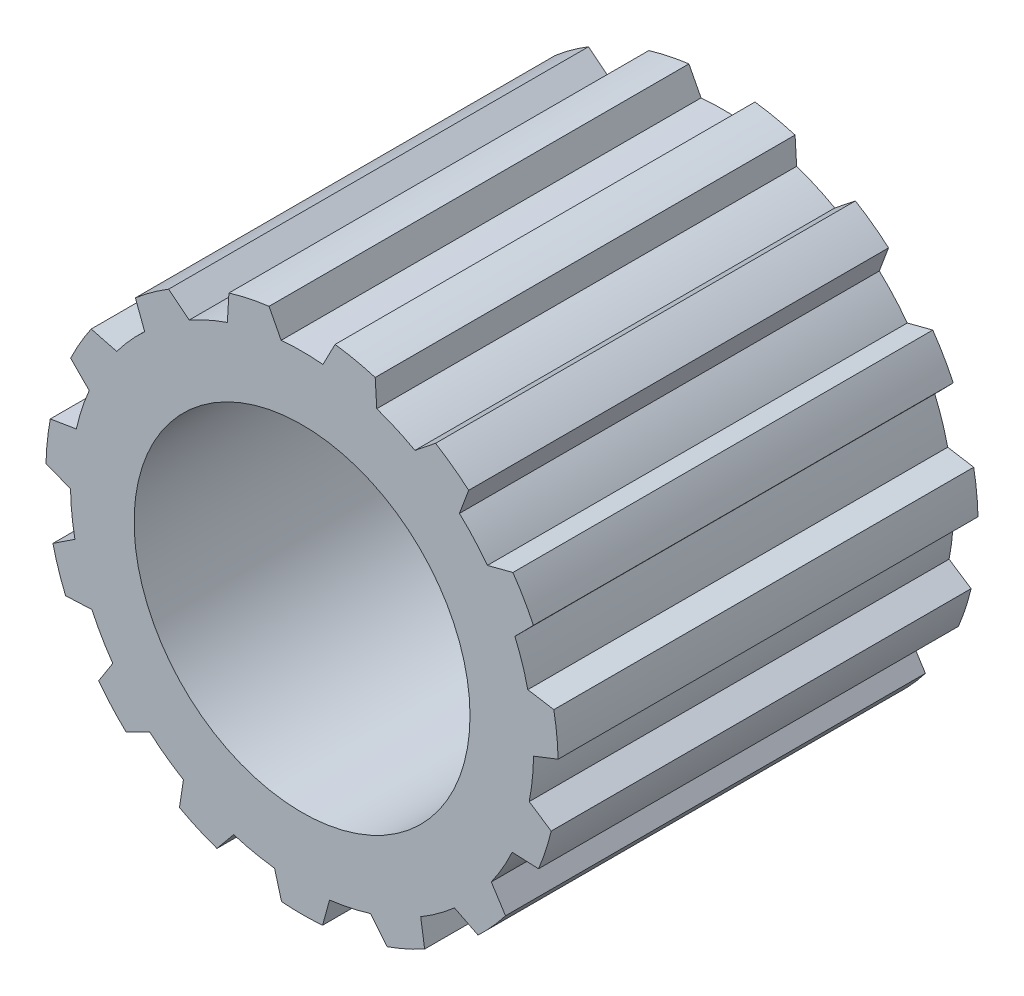
SolidWorks part; units mm, degrees
material "Alumine"
ref_plane "Plan de face" through (0, 0, 0) normal (0, 0, 1) x (1, 0, 0)
ref_plane "Plan de dessus" through (0, 0, 0) normal (0, 1, 0) x (1, 0, 0)
ref_plane "Plan de droite" through (0, 0, 0) normal (1, 0, 0) x (0, 0, -1)
sketch "Esquisse1" plane through (0, 0, 0) normal (0, 0, 1) x (1, 0, 0)
  circle A0 centre (0, 0) radius 6.1
  circle A1 centre (0, 0) radius 4
  dimension "D1" = 12.2
  dimension "D2" = 8
extrude "Boss.-Extru.1" add sketch "Esquisse1" along normal blind 10 contours A1 | A0
sketch "Esquisse3" plane through (0, 0, 0) normal (0, 0, 1) x (1, 0, 0)
  line L0 (0, 0) -> (0, 6.1)
  line L1 (-0.4975, 5.4917) -> (-0.7864, 6.0491)
  line L2 (0.4975, 5.4917) -> (0.7864, 6.0491)
  line L3 (2.6881, 4.8146) -> (3.1788, 5.2063)
  line L4 (1.7792, 5.2193) -> (1.7419, 5.846)
  line L5 (4.414, 3.305) -> (5.0216, 3.4632)
  line L6 (3.7483, 4.0444) -> (3.9691, 4.6321)
  line L7 (5.3766, 1.2239) -> (5.996, 1.1213)
  line L8 (5.0692, 2.1701) -> (5.51, 2.6172)
  line L9 (5.4096, -1.0688) -> (5.9338, -1.4144)
  line L10 (5.5136, -0.0793) -> (6.0982, 0.1498)
  line L11 (4.5072, -3.1767) -> (4.8455, -3.7056)
  line L12 (5.0047, -2.315) -> (5.6319, -2.3435)
  line L13 (2.8255, -4.7353) -> (2.9193, -5.3561)
  line L14 (3.6304, -4.1505) -> (4.1918, -4.4316)
  line L15 (0.6552, -5.4751) -> (0.4884, -6.0804)
  line L16 (1.6284, -5.2683) -> (2.0269, -5.7534)
  line L17 (-1.6284, -5.2683) -> (-2.0269, -5.7534)
  line L18 (-0.6552, -5.4751) -> (-0.4884, -6.0804)
  line L19 (-3.6304, -4.1505) -> (-4.1918, -4.4316)
  line L20 (-2.8255, -4.7353) -> (-2.9193, -5.3561)
  line L21 (-5.0047, -2.315) -> (-5.6319, -2.3435)
  line L22 (-4.5072, -3.1767) -> (-4.8455, -3.7056)
  line L23 (-5.5136, -0.0793) -> (-6.0982, 0.1498)
  line L24 (-5.4096, -1.0688) -> (-5.9338, -1.4144)
  line L25 (-5.0692, 2.1701) -> (-5.51, 2.6172)
  line L26 (-5.3766, 1.2239) -> (-5.996, 1.1213)
  line L27 (-3.7483, 4.0444) -> (-3.9691, 4.6321)
  line L28 (-4.414, 3.305) -> (-5.0216, 3.4632)
  line L29 (-1.7792, 5.2193) -> (-1.7419, 5.846)
  line L30 (-2.6881, 4.8146) -> (-3.1788, 5.2063)
  circle A0 centre (0, 0) radius 6.1 construction
  arc A1 (-0.4975, 5.4917) -> (0.4975, 5.4917) centre (0, 0) cw
  arc A2 (-0.7864, 6.0491) -> (0.7864, 6.0491) centre (0, 0) cw
  arc A3 (1.7419, 5.846) -> (3.1788, 5.2063) centre (0, 0) cw
  arc A4 (1.7792, 5.2193) -> (2.6881, 4.8146) centre (0, 0) cw
  arc A5 (3.9691, 4.6321) -> (5.0216, 3.4632) centre (0, 0) cw
  arc A6 (3.7483, 4.0444) -> (4.414, 3.305) centre (0, 0) cw
  arc A7 (5.51, 2.6172) -> (5.996, 1.1213) centre (0, 0) cw
  arc A8 (5.0692, 2.1701) -> (5.3766, 1.2239) centre (0, 0) cw
  arc A9 (6.0982, 0.1498) -> (5.9338, -1.4144) centre (0, 0) cw
  arc A10 (5.5136, -0.0793) -> (5.4096, -1.0688) centre (0, 0) cw
  arc A11 (5.6319, -2.3435) -> (4.8455, -3.7056) centre (0, 0) cw
  arc A12 (5.0047, -2.315) -> (4.5072, -3.1767) centre (0, 0) cw
  arc A13 (4.1918, -4.4316) -> (2.9193, -5.3561) centre (0, 0) cw
  arc A14 (3.6304, -4.1505) -> (2.8255, -4.7353) centre (0, 0) cw
  arc A15 (2.0269, -5.7534) -> (0.4884, -6.0804) centre (0, 0) cw
  arc A16 (1.6284, -5.2683) -> (0.6552, -5.4751) centre (0, 0) cw
  arc A17 (-0.4884, -6.0804) -> (-2.0269, -5.7534) centre (0, 0) cw
  arc A18 (-0.6552, -5.4751) -> (-1.6284, -5.2683) centre (0, 0) cw
  arc A19 (-2.9193, -5.3561) -> (-4.1918, -4.4316) centre (0, 0) cw
  arc A20 (-2.8255, -4.7353) -> (-3.6304, -4.1505) centre (0, 0) cw
  arc A21 (-4.8455, -3.7056) -> (-5.6319, -2.3435) centre (0, 0) cw
  arc A22 (-4.5072, -3.1767) -> (-5.0047, -2.315) centre (0, 0) cw
  arc A23 (-5.9338, -1.4144) -> (-6.0982, 0.1498) centre (0, 0) cw
  arc A24 (-5.4096, -1.0688) -> (-5.5136, -0.0793) centre (0, 0) cw
  arc A25 (-5.996, 1.1213) -> (-5.51, 2.6172) centre (0, 0) cw
  arc A26 (-5.3766, 1.2239) -> (-5.0692, 2.1701) centre (0, 0) cw
  arc A27 (-5.0216, 3.4632) -> (-3.9691, 4.6321) centre (0, 0) cw
  arc A28 (-4.414, 3.305) -> (-3.7483, 4.0444) centre (0, 0) cw
  arc A29 (-3.1788, 5.2063) -> (-1.7419, 5.846) centre (0, 0) cw
  arc A30 (-2.6881, 4.8146) -> (-1.7792, 5.2193) centre (0, 0) cw
  point P69 (0, 0)
  dimension "D1" = 15
extrude "Enlèv. mat.-Extru.1" cut sketch "Esquisse3" along normal blind 12 and the other way blind 1 contours L22 A22 L21 A21 | L24 A24 L23 A23 | A28 L27 A27 L28 | A30 L29 A29 L30 | L2 A2 L1 A1 | L3 A3 L4 A4 | L6 A5 L5 A6 | L25 A25 L26 A26 | A7 L7 A8 L8 | L10 A9 L9 A10 | L12 A11 L11 A12 | A14 L13 A13 L14 | A16 L15 A15 L16 | A18 L17 A17 L18 | A19 L19 A20 L20
